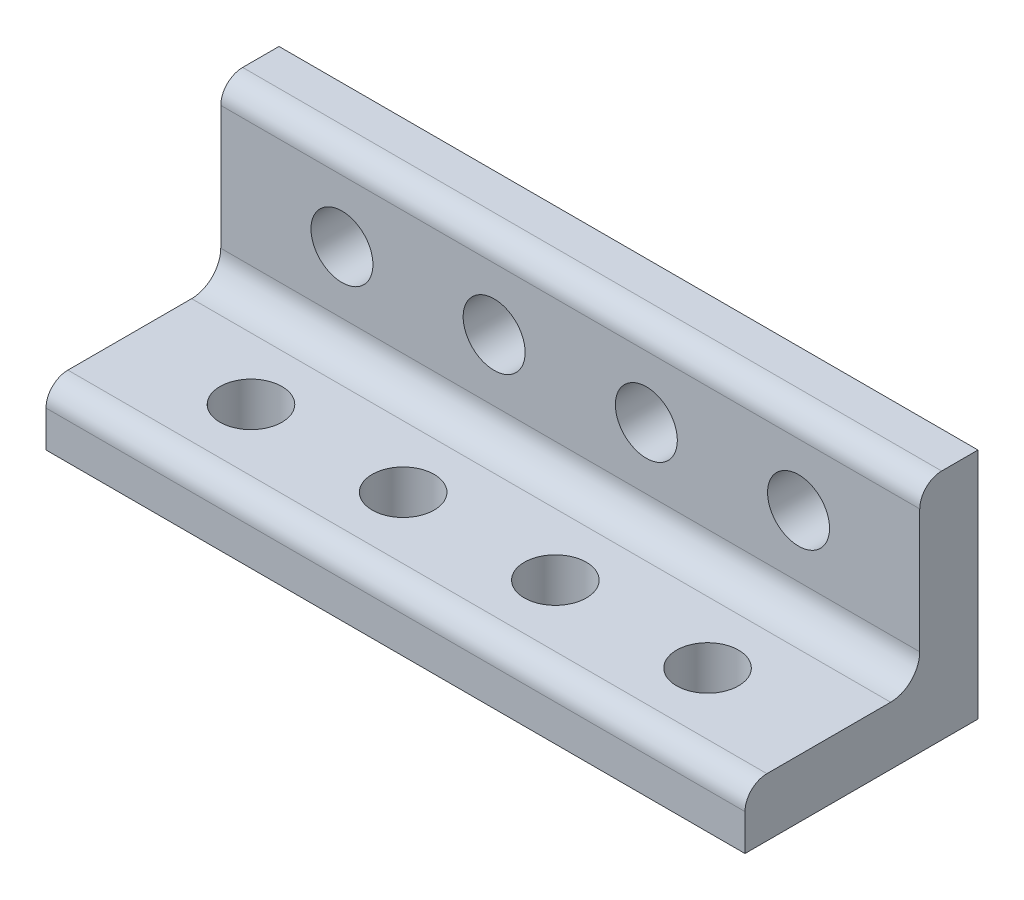
SolidWorks part; units mm, degrees
ref_plane "Front Plane" through (0, 0, 0) normal (0, 0, 1) x (1, 0, 0)
ref_plane "Top Plane" through (0, 0, 0) normal (0, 1, 0) x (1, 0, 0)
ref_plane "Right Plane" through (0, 0, 0) normal (1, 0, 0) x (0, 0, -1)
sketch "Sketch1" plane through (0, 0, 0) normal (0, 1, 0) x (1, 0, 0)
  line L1 (0, 0) -> (76.2, 0)
  line L2 (0, 0) -> (0, 25.4)
  line L3 (0, 25.4) -> (76.2, 25.4)
  line L4 (76.2, 0) -> (76.2, 25.4)
  dimension "D1" = 25.4
  dimension "D2" = 76.2
extrude "Boss-Extrude1" add sketch "Sketch1" along normal blind 6.35
sketch "Sketch2" plane through (0, 0, -25.4) normal (0, 0, -1) x (-1, 0, 0)
  line L1 (0, 0) -> (-76.2, 0)
  line L2 (0, 0) -> (0, 25.4)
  line L3 (0, 25.4) -> (-76.2, 25.4)
  line L4 (-76.2, 0) -> (-76.2, 25.4)
  dimension "D1" = 25.4
  dimension "D2" = 76.2
extrude "Boss-Extrude2" add sketch "Sketch2" against normal blind 6.35
fillet "Fillet1" radius 3.175 1 edges at (38.1, 6.35, -19.05)
fillet "Fillet2" radius 2.3876 2 edges at (38.1, 6.35, 0) (38.1, 25.4, -19.05)
sketch "Sketch3" plane through (0, 6.35, 0) normal (0, 1, 0) x (1, 0, 0)
  line L0 (76.2, 15.875) -> (0, 15.875) construction
  line L1 (0, 15.875) -> (0, 2.3876) construction
  line L3 (76.2, 2.3876) -> (76.2, 15.875) construction
  circle A0 centre (13.2131, 9.1313) radius 3.3782
  circle A1 centre (29.8044, 9.1313) radius 3.3782
  circle A2 centre (46.3956, 9.1313) radius 3.3782
  circle A3 centre (62.9869, 9.1313) radius 3.3782
  point P17 (76.2, 9.1313)
  dimension "D1" = 6.7564
  dimension "D2" = 6.7564
  dimension "D3" = 6.7564
  dimension "D4" = 6.7564
  dimension "D5" = 13.2131
  dimension "D11" = 6.7437
  dimension "D6" = 16.5913
  dimension "D7" = 16.5913
  dimension "D8" = 16.5913
  dimension "D9" = 13.2131
  dimension "D10" = 6.7437
  dimension "D12" = 6.7437
extrude "Cut-Extrude1" cut sketch "Sketch3" against normal through all
sketch "Sketch4" plane through (0, 0, -19.05) normal (0, 0, 1) x (1, 0, 0)
  line L0 (0, 9.525) -> (76.2, 9.525) construction
  line L1 (76.2, 23.0124) -> (76.2, 9.525) construction
  circle A0 centre (13.2131, 16.2687) radius 3.3782
  circle A1 centre (29.8044, 16.2687) radius 3.3782
  circle A2 centre (46.3956, 16.2687) radius 3.3782
  circle A3 centre (62.9869, 16.2687) radius 3.3782
  dimension "D1" = 6.7564
  dimension "D2" = 6.7564
  dimension "D3" = 6.7564
  dimension "D4" = 6.7564
  dimension "D5" = 6.7437
  dimension "D6" = 6.7437
  dimension "D7" = 6.7437
  dimension "D8" = 6.7437
  dimension "D9" = 16.5913
  dimension "D10" = 16.5913
  dimension "D11" = 16.5913
  dimension "D12" = 13.2131
extrude "Cut-Extrude2" cut sketch "Sketch4" against normal through all
